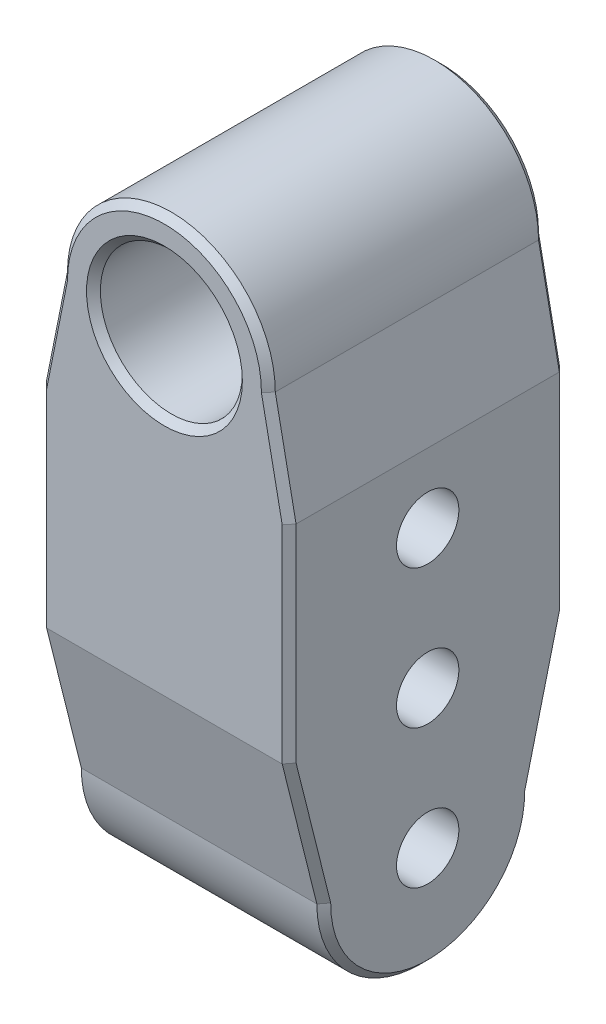
SolidWorks part; units mm, degrees
material "ABS"
ref_plane "前视基准面" through (0, 0, 0) normal (0, 0, 1) x (1, 0, 0)
ref_plane "上视基准面" through (0, 0, 0) normal (0, 1, 0) x (1, 0, 0)
ref_plane "右视基准面" through (0, 0, 0) normal (1, 0, 0) x (0, 0, -1)
sketch "草图1" plane through (0, 0, 0) normal (0, 0, 1) x (1, 0, 0)
  line L0 (0, 15) -> (0, -80) construction
  line L1 (0, -80) -> (18, -80)
  line L2 (0, -80) -> (-18, -80)
  line L3 (-18, -80) -> (-18, -15)
  line L4 (-18, -15) -> (-15, 0)
  line L5 (18, -80) -> (18, -15)
  line L6 (18, -15) -> (15, 0)
  arc A0 (15, 0) -> (-15, 0) centre (0, 0) ccw
  circle A1 centre (0, 0) radius 10.25
  dimension "D1" = 20.5
extrude "凸台-拉伸1" add sketch "草图1" along normal mid plane 40
sketch "草图2" plane through (0, 0, 0) normal (1, 0, 0) x (0, 0, -1)
  line L0 (0, -80) -> (0, -45) construction
  line L1 (-20, -80) -> (20, -80) construction
  line L2 (0, -45) -> (0, -25) construction
  line L3 (-20, 15) -> (-20, -15) construction
  line L4 (-20, -80) -> (-20, -15) construction
  line L5 (-20, -15) -> (-20, 0) construction
  line L6 (-20, -15) -> (-20, -35) construction
  line L7 (20, -15) -> (20, -35) construction
  line L8 (0, -45) -> (0, -65) construction
  line L9 (20, -80) -> (20, -15) construction
  line L10 (-20, -35) -> (-15, -65)
  line L11 (20, -35) -> (15, -65)
  circle A0 centre (0, -45) radius 4.5
  circle A1 centre (0, -25) radius 4.5
  circle A3 centre (0, -65) radius 4.5
  arc A4 (-15, -65) -> (15, -65) centre (0, -65) ccw
extrude "切除-拉伸1" cut sketch "草图2" against normal mid plane 40 contours A1 | A0 | A3
sketch "草图7" plane through (18, 0, 0) normal (1, 0, 0) x (0, 0, -1)
  line L0 (-20, -15) -> (-20, -45) construction
  line L1 (-20, -80) -> (-20, -15) construction
  line L2 (-20, -45) -> (-15, -65)
  line L3 (20, -15) -> (20, -45) construction
  line L4 (20, -80) -> (20, -15) construction
  line L5 (20, -45) -> (15, -65)
  arc A0 (-15, -65) -> (15, -65) centre (0, -65) ccw
extrude "切除-拉伸2" cut sketch "草图7" against normal through all and the other way through all
sketch "草图8" plane through (0, 0, 0) normal (0, 0, 1) x (1, 0, 0)
  line L0 (0, 0) -> (0, -100)
chamfer "倒角1" distance 1 angle 45 18 edges at (10.25, 0, -20) (10.25, 0, 20) (-16.5, -7.5, 20) (-18, -30, 20) (-18, -55, 17.5) (-18, -80, 0) (-18, -55, -17.5) (-18, -30, -20) (-16.5, -7.5, -20) (0, 15, -20) (16.5, -7.5, -20) (18, -30, -20) (18, -55, -17.5) (18, -80, 0) (18, -55, 17.5) (18, -30, 20) (16.5, -7.5, 20) (0, 15, 20)
